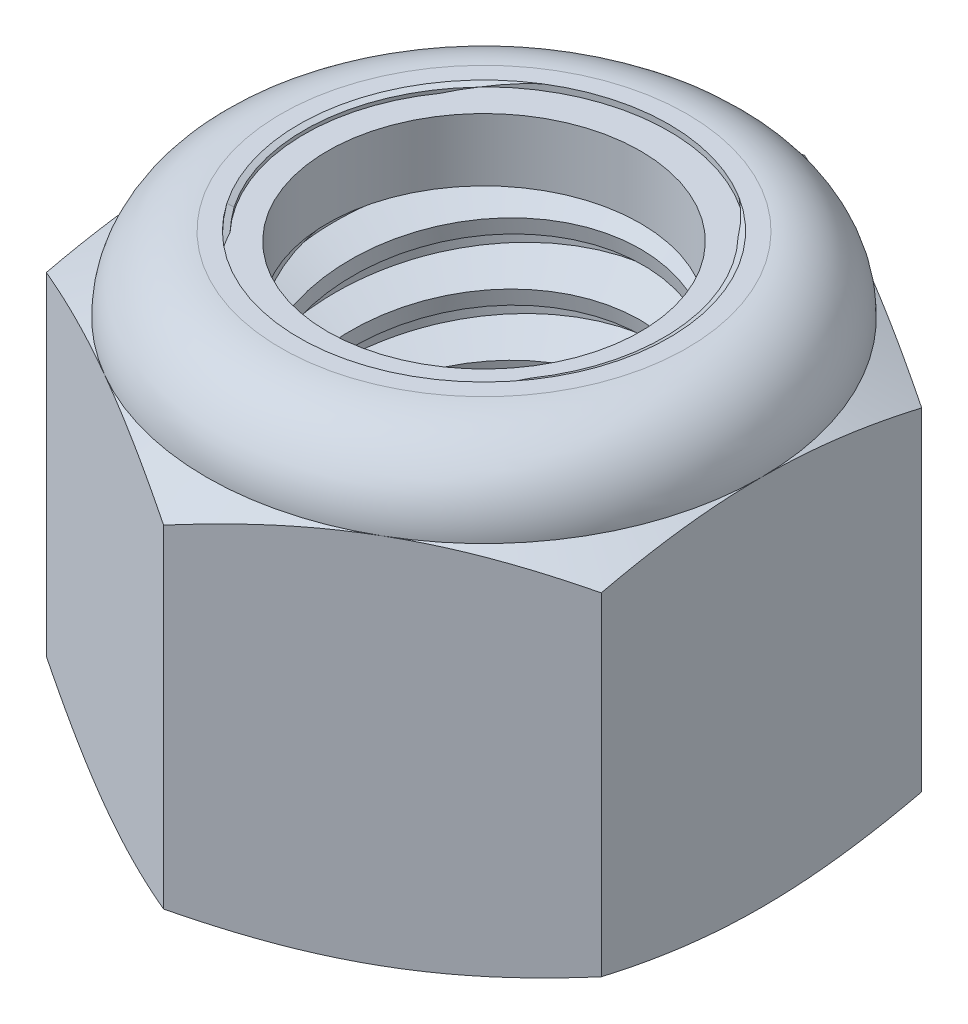
SolidWorks part; units mm, degrees
material "Cast Alloy Steel"
ref_plane "Front" through (0, 0, 0) normal (0, 0, 1) x (1, 0, 0)
ref_plane "Top" through (0, 0, 0) normal (0, 1, 0) x (1, 0, 0)
ref_plane "Right" through (0, 0, 0) normal (1, 0, 0) x (0, 0, -1)
sketch "Sketch1" plane through (0, 0, 0) normal (0, 1, 0) x (1, 0, 0)
  line L1 (0, 8.2489) -> (-7.1438, 4.1244)
  line L2 (-7.1438, 4.1244) -> (-7.1438, -4.1244)
  line L3 (-7.1438, -4.1244) -> (0, -8.2489)
  line L4 (0, -8.2489) -> (7.1437, -4.1244)
  line L5 (7.1437, -4.1244) -> (7.1437, 4.1244)
  line L6 (7.1437, 4.1244) -> (0, 8.2489)
  circle A0 centre (0, 0) radius 7.1438 construction
  dimension "Hex Flats" = 14.2875
extrude "Extrude1" add sketch "Sketch1" along normal blind 11.5094
sketch "Sketch2" plane through (0, 0, 0) normal (1, 0, 0) x (0, 0, -1)
  line L0 (-4.7625, 0) -> (-4.7625, 11.5094) construction
  line L1 (0, 0) -> (4.7625, 0)
  line L2 (0, 0) -> (0, 11.5094)
  line L3 (0, 11.5094) -> (4.7625, 11.5094)
  line L4 (4.7625, 0) -> (4.7625, 11.5094)
  line L5 (-4.1244, 11.5094) -> (4.1244, 11.5094) construction
  line L7 (0, -4.7625) -> (0, 0) construction
  dimension "Thread Dia" = 9.525
revolve "Revolve1" add sketch "Sketch2" angle 360 about L7
sketch "Sketch3" plane through (0, 0, 0) normal (1, 0, 0) x (0, 0, -1)
  line L0 (4.7625, 11.5094) -> (-4.7625, 11.5094) construction
  line L1 (-4.7625, 11.5094) -> (-4.7625, 9.9219) construction
  line L2 (-4.7625, 9.9219) -> (4.7625, 11.5094) construction
  line L3 (4.7625, 11.5094) -> (4.7951, 11.3136) construction
  line L4 (4.7951, 11.3136) -> (5.0235, 9.9435)
  line L5 (5.0235, 9.9435) -> (4.0944, 10.2916)
  line L6 (4.0944, 10.2916) -> (4.0291, 10.683)
  line L7 (4.0291, 10.683) -> (4.7951, 11.3136)
  line L8 (4.0617, 10.4873) -> (4.9093, 10.6286) construction
  line L9 (4.7625, 11.5094) -> (4.7625, 10.6041) construction
  line L10 (4.7625, 10.6041) -> (-4.7625, 9.0166) construction
  line L11 (-4.7625, 9.0166) -> (-4.7625, 9.9219) construction
  line L12 (-0.2832, 11.5094) -> (0.2832, 8.1113) construction
  line L13 (-4.7625, 0) -> (-4.7625, 11.5094) construction
  line L14 (0, 11.5094) -> (4.7625, 11.5094) construction
  line L15 (4.7625, 0) -> (4.7625, 11.5094) construction
  point P13 (0, 9.8103)
  dimension "D1" = 0.1984
  dimension "D2" = 0.3969
  dimension "Thread Pitch" = 1.5875
  dimension "D4" = 60
  dimension "D5" = 1.5875
revolve "Cut-Revolve1" cut sketch "Sketch3" angle 360 about L12
pattern_linear "LPattern1" count 7 spacing 1.5875 along (0, -1, 0) count 2 spacing 1.5875 along (0, 1, 0) of "Cut-Revolve1"
sketch "Sketch4" plane through (0, 0, 0) normal (1, 0, 0) x (0, 0, -1)
  line L0 (0, 11.5094) -> (4.7625, 11.5094)
  line L1 (4.7625, 11.5094) -> (4.0291, 11.1674)
  line L2 (4.0291, 11.1674) -> (4.0291, 0.342)
  line L3 (4.0291, 0.342) -> (4.7625, 0)
  line L4 (4.7625, 0) -> (0, 0)
  line L5 (0, 0) -> (0, 11.5094)
  line L6 (4.7625, 0) -> (4.7625, 11.5094) construction
  line L7 (0, 11.5094) -> (4.7625, 11.5094) construction
  line L8 (0, 0) -> (4.7625, 0) construction
  line L9 (0, 0) -> (0, 11.5094) construction
  line L10 (0, 11.5094) -> (0, 12.3186) construction
  dimension "D1" = 25
revolve "Cut-Revolve2" cut sketch "Sketch4" angle 360 about L10
combine bodies "Combine1" operation type subtract main body 112 bodies to subtract 111
sketch "Sketch5" plane through (0, 0, 0) normal (1, 0, 0) x (0, 0, -1)
  line L0 (0, 0) -> (7.1438, 0)
  line L1 (7.1438, 0) -> (8.2489, 0.5153)
  line L2 (8.2489, 0.5153) -> (8.2489, 9.0758)
  line L3 (8.2489, 9.0758) -> (7.1438, 9.5911)
  line L4 (5.2255, 11.5094) -> (5.2255, 12.7794)
  line L5 (5.2255, 12.7794) -> (9.5189, 12.7794)
  line L6 (9.5189, 12.7794) -> (9.5189, -1.27)
  line L7 (9.5189, -1.27) -> (0, -1.27)
  line L8 (0, -1.27) -> (0, 0)
  line L9 (7.1438, 9.5911) -> (7.1438, 0) construction
  line L10 (0, 0) -> (4.7625, 0) construction
  line L13 (8.2489, 4.7956) -> (9.5189, 4.7956) construction
  line L14 (8.2489, 11.5094) -> (8.2489, 0) construction
  line L15 (0, 0) -> (0, 12.7794) construction
  line L20 (0, 12.7794) -> (5.2255, 12.7794) construction
  line L22 (0, 11.5094) -> (4.7625, 11.5094) construction
  arc A0 (7.1438, 9.5911) -> (5.2255, 11.5094) centre (5.2255, 9.5911) ccw
  dimension "D1" = 25
  dimension "D2" = 1.27
  dimension "D3" = 11.5094
  dimension "D4" = 1.9182
revolve "Cut-Revolve3" cut sketch "Sketch5" angle 360 about L15
sketch "Sketch6" plane through (0, 0, 0) normal (1, 0, 0) x (0, 0, -1)
  line L0 (0, 9.5911) -> (6.9914, 9.5911)
  line L1 (5.2255, 11.357) -> (4.6273, 11.357)
  line L2 (0, 12.7794) -> (0, 9.5911)
  line L3 (4.6273, 12.7794) -> (0, 12.7794)
  line L4 (0, 12.7794) -> (5.2255, 12.7794) construction
  line L5 (0, 0) -> (0, 12.7794) construction
  line L6 (0, 12.7794) -> (0, 44.323) construction
  line L7 (4.6273, 11.357) -> (4.6273, 12.7794)
  line L8 (5.2255, 11.5094) -> (5.2255, 11.357) construction
  line L9 (4.6273, 11.357) -> (4.0291, 11.357) construction
  line L10 (4.0291, 11.357) -> (4.0291, 11.1674) construction
  arc A0 (6.9914, 9.5911) -> (5.2255, 11.357) centre (5.2255, 9.5911) ccw
  arc A1 (7.1438, 9.5911) -> (5.2255, 11.5094) centre (5.2255, 9.5911) ccw construction
  dimension "D1" = 0.1524
revolve "Cut-Revolve4" cut sketch "Sketch6" angle 360 about L6
sketch "Sketch7" plane through (0, 0, 0) normal (1, 0, 0) x (0, 0, -1)
  line L0 (4.0291, 9.6673) -> (6.9134, 9.6673)
  line L1 (5.2255, 11.2808) -> (4.0291, 11.2808)
  line L2 (4.0291, 11.2808) -> (4.0291, 9.6673)
  line L3 (4.0291, 9.6673) -> (0, 9.6673) construction
  line L4 (0, 9.6673) -> (0, 11.2808) construction
  line L5 (0, 11.2808) -> (4.0291, 11.2808) construction
  line L6 (4.0291, 9.6673) -> (4.0291, 9.5911) construction
  line L7 (0, 9.5911) -> (6.9914, 9.5911) construction
  line L8 (5.2255, 11.2808) -> (5.2255, 11.357) construction
  arc A0 (6.9134, 9.6673) -> (5.2255, 11.2808) centre (5.2255, 9.5911) ccw
  arc A2 (6.9914, 9.5911) -> (5.2255, 11.357) centre (5.2255, 9.5911) ccw construction
  dimension "D1" = 0.0762
revolve "Revolve2" add sketch "Sketch7" angle 360 about L4
equation "\"D1@Sketch3\"=\"Thread Pitch@Sketch3\"/8"
equation "\"D2@Sketch3\"=\"Thread Pitch@Sketch3\"/4"
equation "\"D5@Sketch3\"=\"Thread Pitch@Sketch3\""
equation "\"D4@LPattern1\"=\"Thread Pitch@Sketch3\""
equation "\"D3@LPattern1\"=\"Thread Pitch@Sketch3\""
equation "\"D1@LPattern1\"=\"Height@Extrude1\"/\"Thread Pitch@Sketch3\""
equation "\"D4@Sketch5\"=\"Height@Extrude1\"/6"
